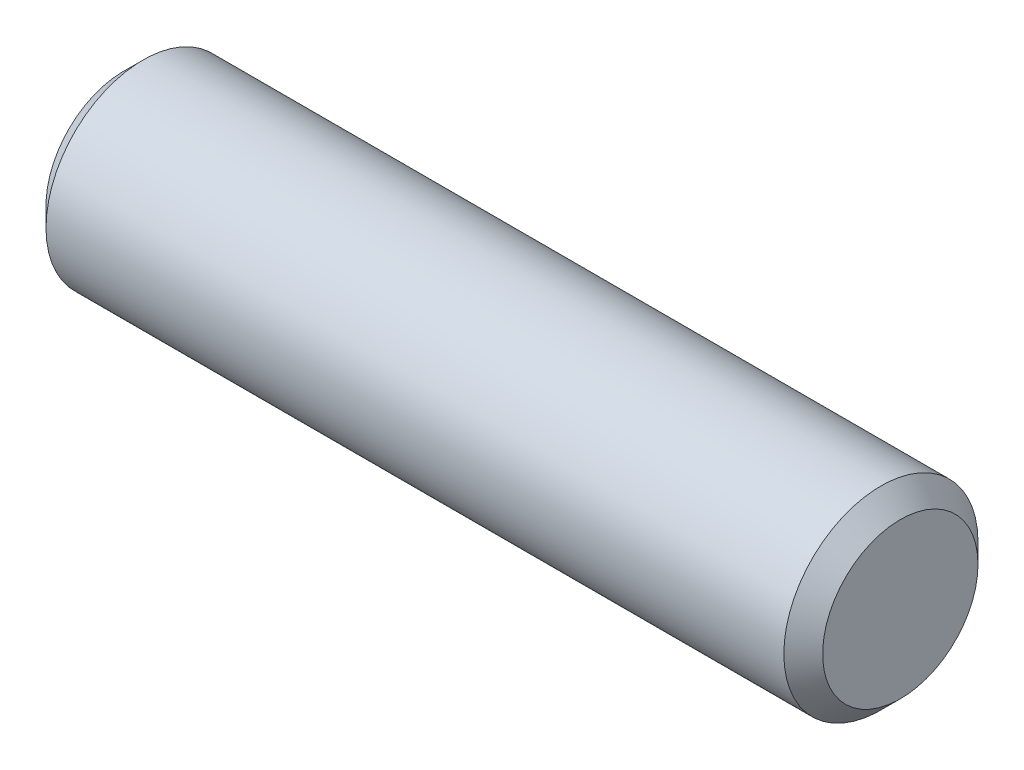
SolidWorks part; units mm, degrees
ref_plane "Front" through (0, 0, 0) normal (0, 0, 1) x (1, 0, 0)
ref_plane "Top" through (0, 0, 0) normal (0, 1, 0) x (1, 0, 0)
ref_plane "Right" through (0, 0, 0) normal (1, 0, 0) x (0, 0, -1)
sketch "Sketch1" plane through (0, 0, 0) normal (0, 0, 1) x (1, 0, 0)
  line L0 (-3.175, 0) -> (3.175, 0) construction
  line L1 (3.175, 0.7937) -> (3.175, -0.7937) construction
  line L2 (-3.175, 0.7937) -> (-3.175, -0.7937) construction
  dimension "Length" = 6.35
  dimension "Diameter" = 1.5875
sketch "Sketch2" plane through (0, 0, 0) normal (1, 0, 0) x (0, 0, -1)
  circle A0 centre (0, 0) radius 0.7937
extrude "Extrude1" add sketch "Sketch2" against normal up to vertex (3.175 mm away) and the other way up to vertex (3.175 mm away) up to point (-3.175, 0.7937, 0) other way up to point (3.175, 0.7937, 0)
chamfer "Chamfer1" distance 0.1588 angle 45 2 edges at (3.175, 0, -0.7937) (-3.175, 0, -0.7937)
equation "\"D1@Chamfer1\" = \"Diameter@Sketch1\"*.1"
